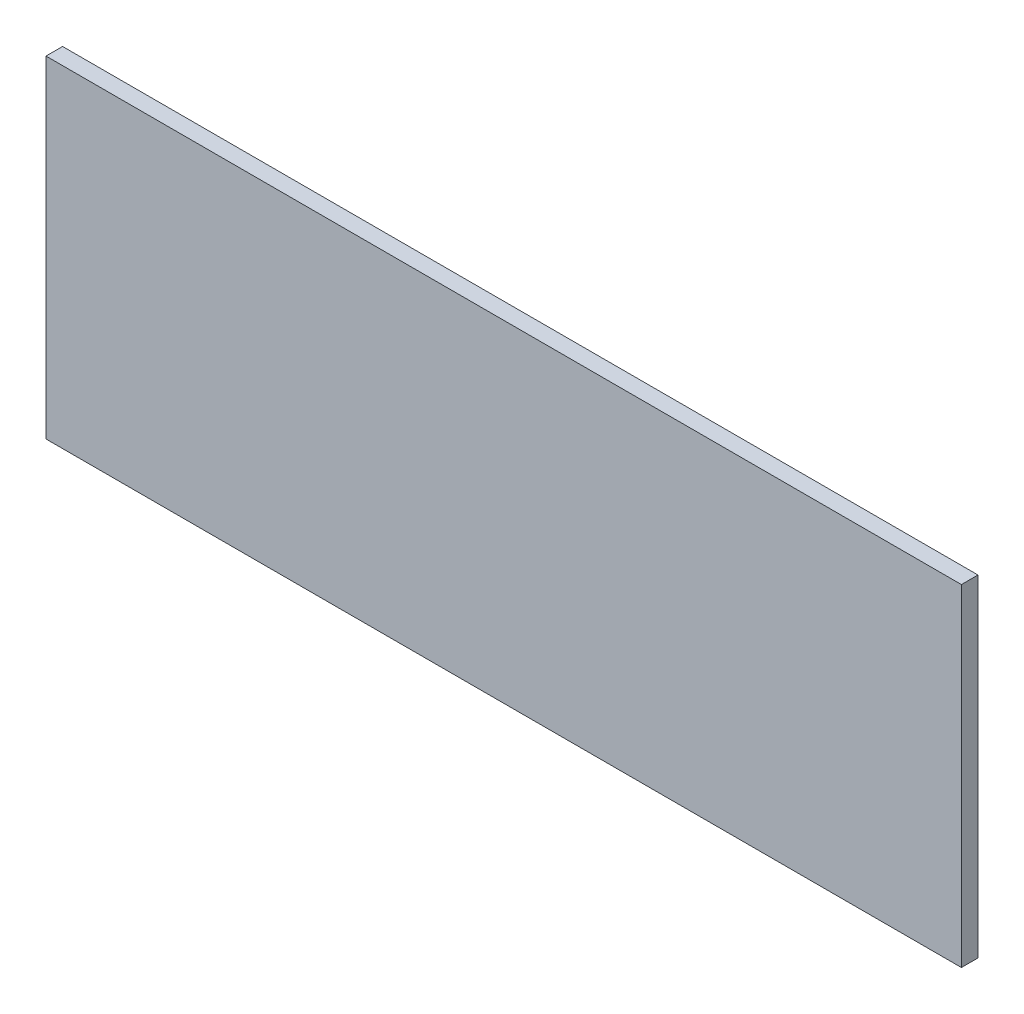
SolidWorks part; units mm, degrees
ref_plane "Front Plane" through (0, 0, 0) normal (0, 0, 1) x (1, 0, 0)
ref_plane "Top Plane" through (0, 0, 0) normal (0, 1, 0) x (1, 0, 0)
ref_plane "Right Plane" through (0, 0, 0) normal (1, 0, 0) x (0, 0, -1)
sketch "Sketch1" plane through (0, 0, 0) normal (0, 0, 1) x (1, 0, 0)
  line L1 (-345, 125) -> (345, 125)
  line L2 (-345, 125) -> (-345, -125)
  line L3 (-345, -125) -> (345, -125)
  line L4 (345, 125) -> (345, -125)
  line L5 (-345, 125) -> (345, -125) construction
  line L6 (-345, -125) -> (345, 125) construction
  point P0 (0, 0)
  dimension "D1" = 690
  dimension "D2" = 250
extrude "Boss-Extrude1" add sketch "Sketch1" along normal blind 12.5
